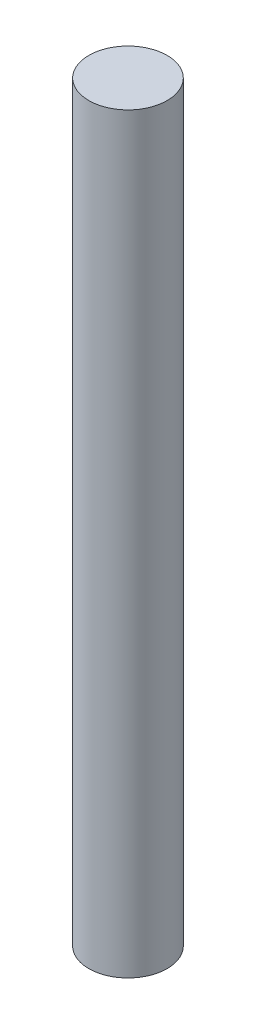
SolidWorks part; units mm, degrees
ref_plane "Front Plane" through (0, 0, 0) normal (0, 0, 1) x (1, 0, 0)
ref_plane "Top Plane" through (0, 0, 0) normal (0, 1, 0) x (1, 0, 0)
ref_plane "Right Plane" through (0, 0, 0) normal (1, 0, 0) x (0, 0, -1)
sketch "Sketch1" plane through (0, 0, 0) normal (0, 1, 0) x (1, 0, 0)
  circle A0 centre (0, 0) radius 3.9688
  dimension "D1" = 7.9375
extrude "Boss-Extrude1" add sketch "Sketch1" along normal blind 76.2
